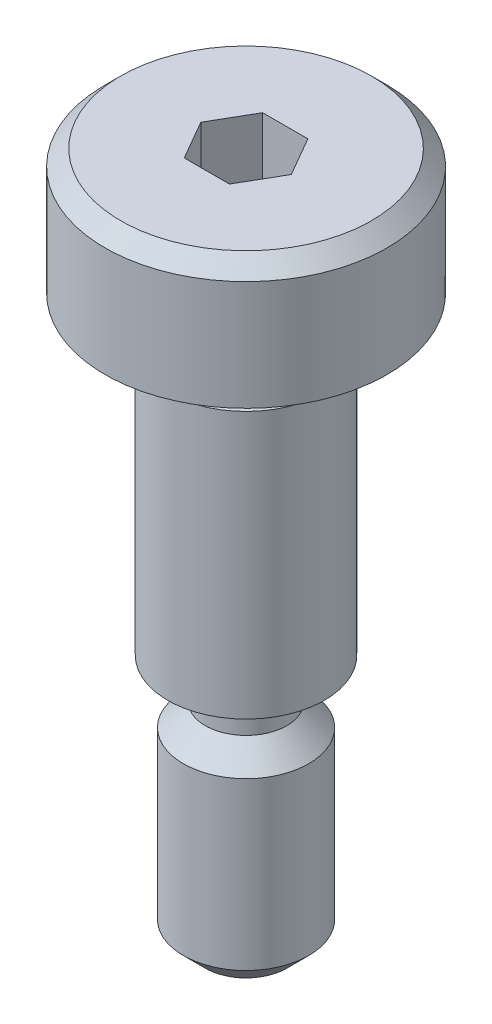
SolidWorks part; units mm, degrees
ref_plane "Front plane" through (0, 0, 0) normal (0, 0, 1) x (1, 0, 0)
ref_plane "Top plane" through (0, 0, 0) normal (0, 1, 0) x (1, 0, 0)
ref_plane "Right Plane" through (0, 0, 0) normal (1, 0, 0) x (0, 0, -1)
sketch "Sketch1" plane through (0, 0, 0) normal (0, 0, 1) x (1, 0, 0)
  line L0 (0, 0) -> (0, 22)
  line L1 (0, 22) -> (4, 22)
  line L2 (4, 22) -> (4.5, 21.5)
  line L3 (4.5, 21.5) -> (4.5, 18)
  line L4 (4.5, 18) -> (2.5, 18)
  line L5 (2, 17.5) -> (2, 17)
  line L6 (2, 17) -> (2.5, 16.5)
  line L7 (2.5, 16.5) -> (2.5, 8)
  line L8 (2.5, 8) -> (2, 8)
  line L9 (1.3, 7.3) -> (1.3, 6.7)
  line L10 (1.3, 6.7) -> (2, 6)
  line L11 (2, 6) -> (2, 0.7)
  line L12 (2, 0.7) -> (1.3, 0)
  line L13 (1.3, 0) -> (0, 0)
  arc A0 (2.5, 18) -> (2, 17.5) centre (2.5, 17.5) ccw
  arc A1 (2, 8) -> (1.3, 7.3) centre (2, 7.3) ccw
  dimension "D9" = 1.5
  dimension "D1" = 2
  dimension "D2" = 4.5
  dimension "D3" = 2.5
  dimension "D4" = 4
  dimension "D5" = 135
  dimension "D6" = 0.5
  dimension "D7" = 10
  dimension "D8" = 0.5
  dimension "D10" = 0.7
  dimension "D11" = 8
  dimension "D12" = 2
revolve "Revolve1" add sketch "Sketch1" angle 360 about L0
sketch "Sketch2" plane through (0, 22, 0) normal (0, 1, 0) x (1, 0, 0)
  line L1 (0.7217, 1.25) -> (-0.7217, 1.25)
  line L2 (-0.7217, 1.25) -> (-1.4434, 0)
  line L3 (-1.4434, 0) -> (-0.7217, -1.25)
  line L4 (-0.7217, -1.25) -> (0.7217, -1.25)
  line L5 (0.7217, -1.25) -> (1.4434, 0)
  line L6 (1.4434, 0) -> (0.7217, 1.25)
  circle A0 centre (0, 0) radius 1.25 construction
  dimension "D1" = 2.5
extrude "Cut-Extrude1" cut sketch "Sketch2" against normal blind 3
